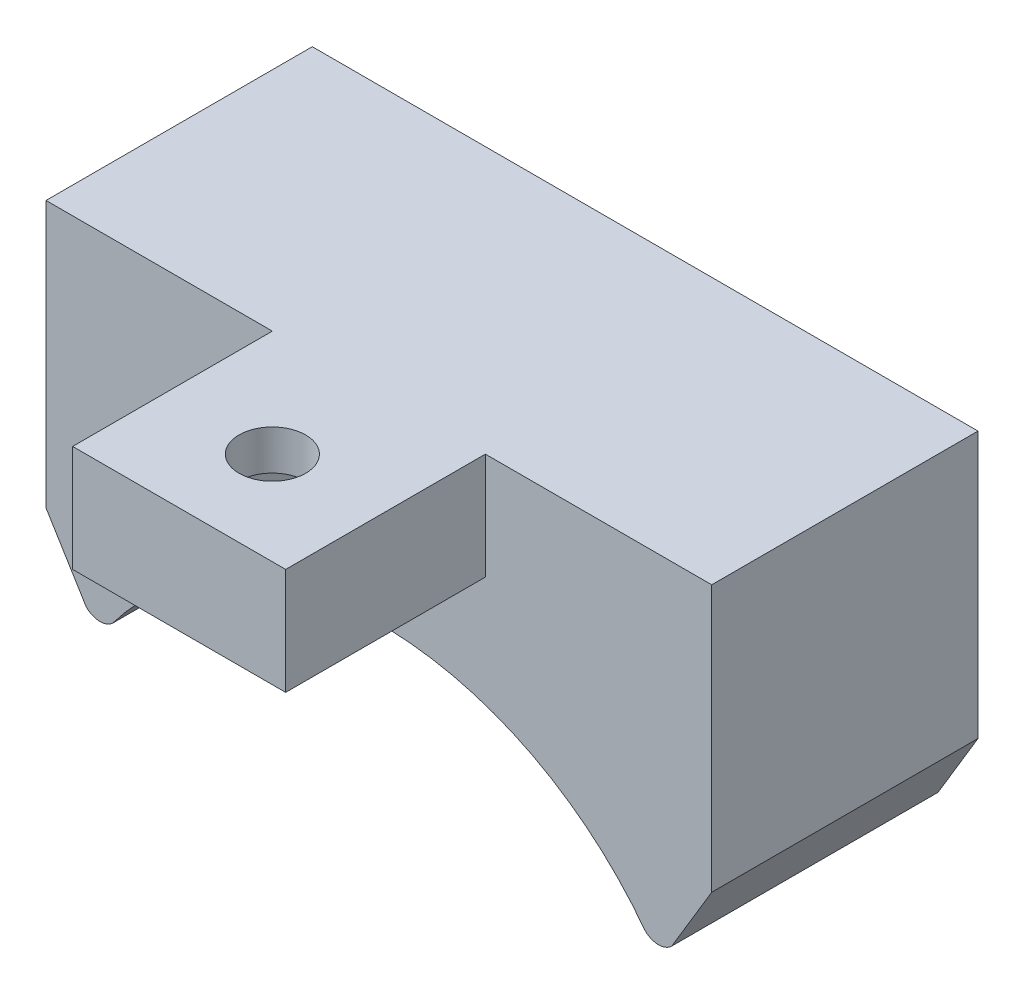
SolidWorks part; units mm, degrees
ref_plane "Front Plane" through (0, 0, 0) normal (0, 0, 1) x (1, 0, 0)
ref_plane "Top Plane" through (0, 0, 0) normal (0, 1, 0) x (1, 0, 0)
ref_plane "Right Plane" through (0, 0, 0) normal (1, 0, 0) x (0, 0, -1)
sketch "Sketch1" plane through (0, 0, 0) normal (0, 0, 1) x (1, 0, 0)
  line L0 (0, -5) -> (0, -5.0033)
  line L1 (-25, 10) -> (25, 10)
  line L2 (-25, 10) -> (-25, -10)
  line L3 (-25, -10) -> (-14.9972, -10)
  line L4 (25, 10) -> (25, -10)
  line L5 (-25, 10) -> (25, -10) construction
  line L6 (-25, -10) -> (25, 10) construction
  line L7 (-25, -10) -> (-21.995, -14.9)
  line L8 (22, -15) -> (25, -10)
  line L9 (14.9972, -10) -> (25, -10)
  arc A2 (-20, -15) -> (20, -15) centre (0, -30.0083) cw
  arc A5 (-21.995, -14.9) -> (-20, -15) centre (-20.9475, -13.9525) ccw
  arc A6 (20, -15) -> (22, -15) centre (21, -14) ccw
  point P0 (0, 0)
  point P9 (0, 0)
  point P10 (0, -5)
  dimension "D1" = 50
  dimension "D2" = 20
  dimension "D3" = 5
extrude "Boss-Extrude1" add sketch "Sketch1" along normal blind 20
sketch "Sketch2" plane through (0, 0, 20) normal (0, 0, 1) x (1, 0, 0)
  line L0 (0, 10) -> (-8, 10)
  line L1 (-25, 10) -> (25, 10) construction
  line L2 (-8, 10) -> (-8, 2)
  line L3 (-8, 2) -> (8, 2)
  line L4 (8, 2) -> (8, 10)
  line L5 (8, 10) -> (0, 10)
  dimension "D1" = 8
  dimension "D2" = 8
  dimension "D3" = 8
  dimension "D4" = 8
extrude "Boss-Extrude2" add sketch "Sketch2" along normal blind 15
sketch "Sketch4" plane through (0, 2, 0) normal (0, -1, 0) x (1, 0, 0)
  line L0 (-8, 35) -> (8, 35) construction
  line L2 (2.4573, 23.7559) -> (4.9007, 28.0119)
  line L3 (4.9007, 28.0119) -> (2.4367, 32.2559)
  line L4 (2.4367, 32.2559) -> (-2.4707, 32.2441)
  line L5 (-2.4707, 32.2441) -> (-4.9142, 27.9881)
  line L6 (-4.9142, 27.9881) -> (-2.4502, 23.7441)
  line L7 (-2.4502, 23.7441) -> (2.4573, 23.7559)
  circle A0 centre (-0.0067, 28) radius 4.25 construction
  point P0 (0, 35)
  point P1 (-0.0067, 28)
  dimension "D2" = 7
  dimension "D3" = 8.5
extrude "Cut-Extrude1" cut sketch "Sketch4" against normal blind 5
sketch "Sketch5" plane through (0, 7, 0) normal (0, -1, 0) x (1, 0, 0)
  line L0 (-2.4502, 23.7441) -> (2.4573, 23.7559) construction
  circle A0 centre (0, 28) radius 2.5
  point P4 (0.0036, 23.75)
  dimension "D1" = 4.25
  dimension "D2" = 2.4502
extrude "Cut-Extrude2" cut sketch "Sketch5" against normal up to surface (3 mm away) contours A0 up to face at (0, 10, 18.75)
